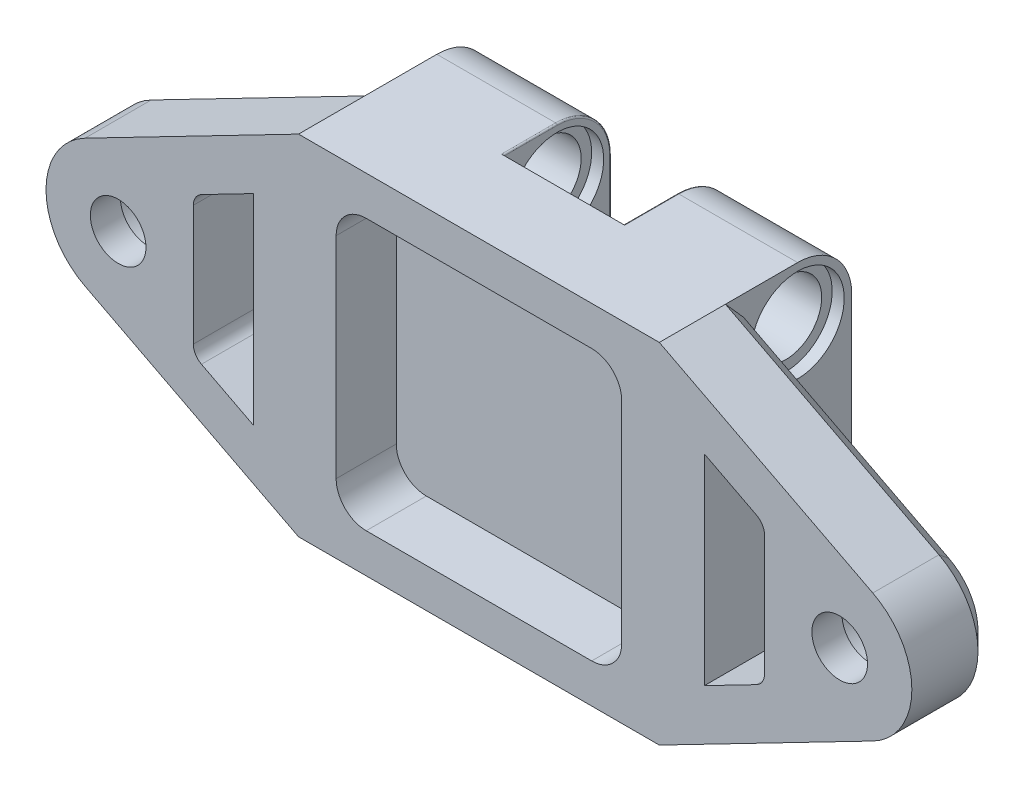
SolidWorks part; units mm, degrees
ref_plane "正面" through (0, 0, 0) normal (0, 0, 1) x (1, 0, 0)
ref_plane "平面" through (0, 0, 0) normal (0, 1, 0) x (1, 0, 0)
ref_plane "右側面" through (0, 0, 0) normal (1, 0, 0) x (0, 0, -1)
sketch "ｽｹｯﾁ2" plane through (0, 0, 0) normal (0, 0, 1) x (1, 0, 0)
  line L0 (-4, 11.6) -> (-12, 11.6) construction
  line L1 (4, -11.6) -> (-4, -11.6) construction
  line L2 (4, -11.6) -> (4, 11.6) construction
  line L3 (4, 11.6) -> (-4, 11.6) construction
  line L4 (-4, -11.6) -> (-4, 11.6) construction
  line L5 (4, -11.6) -> (-4, 11.6) construction
  line L6 (4, 11.6) -> (-4, -11.6) construction
  line L7 (-12, 11.6) -> (-12, -11.6) construction
  line L8 (-12, -11.6) -> (-4, -11.6) construction
  line L9 (4, 11.6) -> (12, 11.6) construction
  line L10 (12, 11.6) -> (12, -11.6) construction
  line L11 (12, -11.6) -> (4, -11.6) construction
  line L12 (-12, 11.6) -> (-26.2026, 4.2648)
  line L13 (-26.2026, -4.2648) -> (-12, -11.6)
  line L14 (26.2026, 4.2648) -> (12, 11.6)
  line L15 (26.2026, -4.2648) -> (12, -11.6)
  line L16 (-12, 11.6) -> (12, 11.6)
  line L17 (12, -11.6) -> (-12, -11.6)
  arc A0 (-26.2026, 4.2648) -> (-26.2026, -4.2648) centre (-24, 0) ccw
  arc A1 (26.2026, 4.2648) -> (26.2026, -4.2648) centre (24, 0) cw
  circle A2 centre (-24, 0) radius 1.85
  circle A3 centre (24, 0) radius 1.85
  circle A4 centre (-24, 0) radius 2.95 construction
  circle A5 centre (24, 0) radius 2.95 construction
  point P0 (0, 0)
  dimension "D4" = 4.8
  dimension "D5" = 3.7
  dimension "D6" = 5.9
  dimension "D1" = 8
  dimension "D2" = 23.2
  dimension "D3" = 48
extrude "ﾎﾞｽ - 押し出し1" add sketch "ｽｹｯﾁ2" along normal blind 5.6
sketch "ｽｹｯﾁ3" plane through (0, 0, 0) normal (0, 0, -1) x (-1, 0, 0)
  circle A0 centre (-24, 0) radius 2.95
  circle A1 centre (24, 0) radius 2.95
  circle A2 centre (-24, 0) radius 2.95 construction
extrude "ｶｯﾄ - 押し出し1" cut sketch "ｽｹｯﾁ3" against normal blind 3.6
sketch "ｽｹｯﾁ4" plane through (0, 0, 0) normal (0, 0, -1) x (-1, 0, 0)
  line L5 (-12, 11.6) -> (-4, 11.6)
  line L6 (-12, 11.6) -> (-12, -11.6)
  line L7 (-12, -11.6) -> (-4, -11.6)
  line L8 (-4, 11.6) -> (-4, -11.6)
  line L9 (-12, 11.6) -> (-4, -11.6) construction
  line L10 (-12, -11.6) -> (-4, 11.6) construction
  line L11 (4, 11.6) -> (12, 11.6)
  line L12 (4, 11.6) -> (4, -11.6)
  line L13 (4, -11.6) -> (12, -11.6)
  line L14 (12, 11.6) -> (12, -11.6)
  line L15 (4, 11.6) -> (12, -11.6) construction
  line L16 (4, -11.6) -> (12, 11.6) construction
  point P4 (-8, 0)
  point P13 (8, 0)
extrude "ﾎﾞｽ - 押し出し2" add sketch "ｽｹｯﾁ4" along normal blind 7.2
ref_plane "平面2" through (0, 0, 0) normal (1, 0, 0) x (0, 0, -1)
sketch "ｽｹｯﾁ5" plane through (0, 0, 0) normal (1, 0, 0) x (0, 0, -1)
  line L0 (3.6, 8) -> (3.6, -8) construction
  line L3 (2.8, 2.2627) -> (2.8, 0.8)
  line L4 (2.8, 0.8) -> (1.3373, 0.8)
  line L5 (3.6, 0) -> (50003.6, 0) construction
  line L8 (4.4, 2.2627) -> (4.4, 0.8)
  line L9 (1.3373, 0.8) -> (5.8627, 0.8) construction
  line L10 (1.3373, 0.8) -> (1.3373, -0.8) construction
  line L11 (1.3373, -0.8) -> (5.8627, -0.8) construction
  line L12 (5.8627, 0.8) -> (5.8627, -0.8) construction
  line L13 (1.3373, 0.8) -> (5.8627, -0.8) construction
  line L14 (1.3373, -0.8) -> (5.8627, 0.8) construction
  line L15 (2.8, 2.2627) -> (4.4, 2.2627) construction
  line L16 (2.8, 2.2627) -> (2.8, -2.2627) construction
  line L17 (2.8, -2.2627) -> (4.4, -2.2627) construction
  line L18 (4.4, 2.2627) -> (4.4, -2.2627) construction
  line L19 (2.8, 2.2627) -> (4.4, -2.2627) construction
  line L20 (2.8, -2.2627) -> (4.4, 2.2627) construction
  line L21 (4.4, 0.8) -> (5.8627, 0.8)
  line L22 (5.8627, -0.8) -> (4.4, -0.8)
  line L23 (4.4, -0.8) -> (4.4, -2.2627)
  line L24 (1.3373, -0.8) -> (2.8, -0.8)
  line L25 (2.8, -0.8) -> (2.8, -2.2627)
  line L26 (7.2, 11.6) -> (0, 11.6) construction
  line L27 (7.2, -11.6) -> (0, -11.6) construction
  line L28 (7.2, 11.6) -> (7.2, -11.6) construction
  line L29 (0, 2.95) -> (0, -2.95) construction
  circle A0 centre (3.6, 8) radius 2.4
  circle A1 centre (3.6, -8) radius 2.4
  circle A2 centre (3.6, 0) radius 2.4 construction
  arc A3 (1.3373, 0.8) -> (1.3373, -0.8) centre (3.6, 0) ccw
  arc A4 (2.8, 2.2627) -> (4.4, 2.2627) centre (3.6, 0) cw
  arc A5 (5.8627, -0.8) -> (5.8627, 0.8) centre (3.6, 0) ccw
  arc A6 (2.8, -2.2627) -> (4.4, -2.2627) centre (3.6, 0) ccw
  point P8 (3.6, 0)
  point P21 (3.6, 0)
  point P26 (3.6, 0)
  dimension "D1" = 4.8
  dimension "D2" = 16
  dimension "D3" = 1.6
extrude "ｶｯﾄ - 押し出し2" cut sketch "ｽｹｯﾁ5" against normal through all both and the other way through all
fillet "ﾌｨﾚｯﾄ1" radius 3.6 4 edges at (8, -11.6, -7.2) (-8, -11.6, -7.2) (-8, 11.6, -7.2) (8, 11.6, -7.2)
sketch "ｽｹｯﾁ6" plane through (4, 0, 0) normal (-1, 0, 0) x (0, 0, 1)
  circle A0 centre (-3.6, 8) radius 3.1
  circle A1 centre (-3.6, -8) radius 3.1
  dimension "D1" = 6.2
  dimension "D2" = 6.2
extrude "ｶｯﾄ - 押し出し3" cut sketch "ｽｹｯﾁ6" against normal blind 0.8
ref_plane "平面3" through (8, 0, 0) normal (1, 0, 0) x (0, 0, -1)
mirror "ﾐﾗｰ1" about plane through (8, 0, 0) normal (1, 0, 0) of "ｶｯﾄ - 押し出し3"
mirror "ﾐﾗｰ2" about plane through (0, 0, 0) normal (1, 0, 0) of "ﾐﾗｰ1", "ｶｯﾄ - 押し出し3"
sketch "ｽｹｯﾁ7" plane through (0, 0, 0) normal (0, 0, -1) x (-1, 0, 0)
  line L3 (-19, 4.6082) -> (-19, -4.6082)
  line L7 (-15, -6.6741) -> (-15, 6.6741)
  line L8 (-15, 6.6741) -> (-24.826, 1.5993)
  line L9 (-24.826, -1.5993) -> (-15, -6.6741)
  line L10 (-15, -6.6741) -> (-15, 6.6741)
  line L11 (-15, 6.6741) -> (-19, 4.6082)
  line L12 (-19, -4.6082) -> (-15, -6.6741)
  arc A2 (-24.826, 1.5993) -> (-24.826, -1.5993) centre (-24, 0) ccw
  dimension "D2" = 4
  dimension "D1" = 3
extrude "ｶｯﾄ - 押し出し4" cut sketch "ｽｹｯﾁ7" against normal through all
sketch "ｽｹｯﾁ8" plane through (0, 0, 5.6) normal (0, 0, 1) x (1, 0, 0)
  line L1 (-9.5, 9) -> (9.5, 9)
  line L2 (-9.5, 9) -> (-9.5, -9)
  line L3 (-9.5, -9) -> (9.5, -9)
  line L4 (9.5, 9) -> (9.5, -9)
  line L5 (-9.5, 9) -> (9.5, -9) construction
  line L6 (-9.5, -9) -> (9.5, 9) construction
  point P4 (0, 0)
  dimension "D1" = 18
  dimension "D2" = 19
extrude "ｶｯﾄ - 押し出し5" cut sketch "ｽｹｯﾁ8" against normal blind 4
fillet "ﾌｨﾚｯﾄ3" radius 2 4 edges at (9.5, -9, 3.6) (9.5, 9, 3.6) (-9.5, -9, 3.6) (-9.5, 9, 3.6)
fillet "ﾌｨﾚｯﾄ4" radius 0.1 10 edges at (-4, 11.6, -1.8) (-4, 10.5456, -6.1456) (-4, -11.6, -1.8) (-4, -10.5456, -6.1456) (4, -11.6, -1.8) (4, -10.5456, -6.1456) (4, 11.6, -1.8) (4, 10.5456, -6.1456) (-4, 0, -7.2) (4, 0, -7.2)
fillet "ﾌｨﾚｯﾄ5" radius 1 2 edges at (19, -4.6082, 2.8) (19, 4.6082, 2.8)
chamfer "面取り1" distance 1 angle 45 6 edges at (16.7294, -5.7809, 0) (19, 0, 0) (16.7294, 5.7809, 0) (15, 0, 0) (18.8541, -4.5194, 0) (18.8541, 4.5194, 0)
mirror "ﾐﾗｰ3" about plane through (0, 0, 0) normal (1, 0, 0) of "面取り1", "ﾌｨﾚｯﾄ5", "ｶｯﾄ - 押し出し4"
chamfer "面取り2" distance 1.2 angle 45 6 edges at (-19.1013, -7.9324, 0) (-28.8, 0, 0) (-19.1013, 7.9324, 0) (19.1013, -7.9324, 0) (28.8, 0, 0) (19.1013, 7.9324, 0)
sketch "ｽｹｯﾁ9" plane through (12, 0, 0) normal (1, 0, 0) x (0, 0, -1)
  line L0 (5.8627, -0.8) -> (4.4, -0.8) construction
  line L1 (4.4, 0.8) -> (4.5, 0.8)
  line L2 (4.4, 0.8) -> (4.4, -0.8)
  line L3 (4.4, -0.8) -> (4.5, -0.8)
  line L4 (4.5, 0.8) -> (4.5, -0.8)
  line L5 (4.4, 0.8) -> (4.5, -0.8) construction
  line L6 (4.4, -0.8) -> (4.5, 0.8) construction
  point P4 (4.45, 0)
  dimension "D1" = 0.1
extrude "ﾎﾞｽ - 押し出し3" add sketch "ｽｹｯﾁ9" against normal blind 8
mirror "ﾐﾗｰ4" about plane through (0, 0, 0) normal (1, 0, 0) of "ﾎﾞｽ - 押し出し3"
